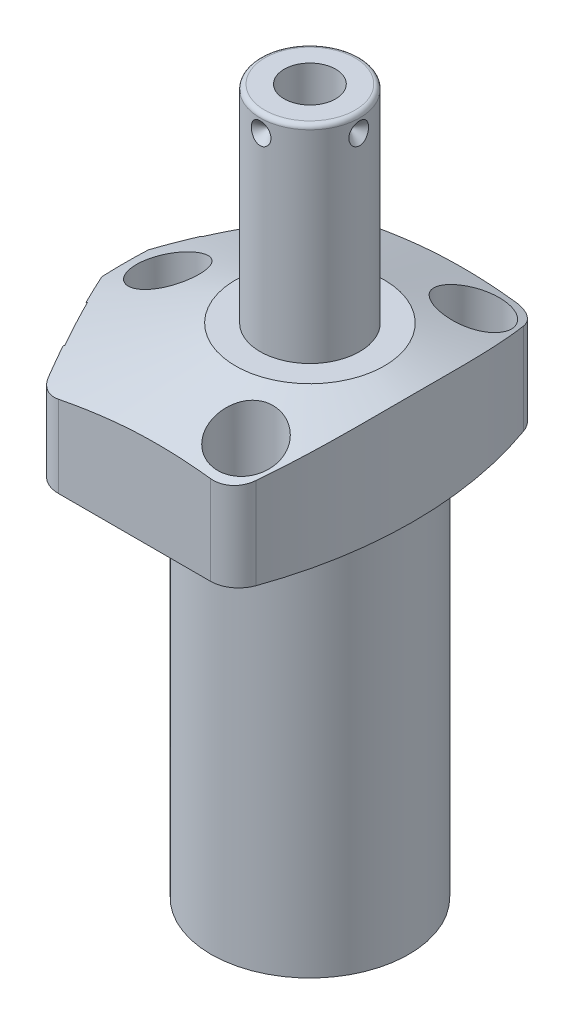
SolidWorks part; units mm, degrees
material "Alloy Steel"
ref_plane "Front Plane" through (0, 0, 0) normal (0, 0, 1) x (1, 0, 0)
ref_plane "Top Plane" through (0, 0, 0) normal (0, 1, 0) x (1, 0, 0)
ref_plane "Right Plane" through (0, 0, 0) normal (1, 0, 0) x (0, 0, -1)
ref_plane "Plane1" through (0, 0, 0) normal (0, 0, 1) x (0, -1, 0)
sketch "Sketch1" plane through (0, 0, 0) normal (0, 0, 1) x (0, -1, 0)
  line L0 (0, 44.45) -> (-26.9748, 44.45)
  line L1 (-26.9748, 44.45) -> (-26.9748, 0)
  line L2 (-26.9748, 0) -> (84.1502, 0)
  line L3 (84.1502, 0) -> (84.1502, 22.098)
  line L4 (84.1502, 22.098) -> (0, 22.098)
  line L5 (0, 22.098) -> (0, 44.45)
  line L6 (-32.531, 0) -> (89.7065, 0) construction
  dimension "D1" = 111.125
  dimension "D2" = 26.9748
  dimension "D3" = 88.9
  dimension "D4" = 44.196
revolve "Revolve1" add sketch "Sketch1" angle 360 about L6
ref_plane "Plane2" through (0, 0, 0) normal (0, -1, 0) x (0, 0, -1)
sketch "Sketch2" plane through (0, 0, 0) normal (0, -1, 0) x (0, 0, -1)
  line L0 (34.1122, -28.4984) -> (34.1122, 28.4984)
  line L2 (-34.1122, 28.4984) -> (-34.1122, -28.4984)
  line L3 (0, -32.1458) -> (0, 48.0974) construction
  arc A0 (34.1122, -28.4984) -> (34.1122, 28.4984) centre (0, 0) ccw
  circle A1 centre (0, 0) radius 44.45
  arc A2 (-34.1122, 28.4984) -> (-34.1122, -28.4984) centre (0, 0) ccw
  point P4 (0, 0)
  dimension "D1" = 68.2244
  dimension "D2" = 0
extrude "Cut-Extrude1" cut sketch "Sketch2" against normal up to next
ref_plane "Plane3" through (0, 0, 0) normal (0, -1, 0) x (-1, 0, 0)
sketch "Sketch3" plane through (0, 0, 0) normal (0, -1, 0) x (-1, 0, 0)
  line L0 (25.9049, 34.1122) -> (44.0427, 0)
  line L1 (44.0427, 0) -> (25.9049, -34.1122)
  line L2 (-39.4859, -20.995) -> (73.8214, 39.2515) construction
  line L3 (0, 0) -> (44.0427, 0) construction
  line L6 (-28.4984, -34.1122) -> (28.4984, -34.1122)
  line L7 (28.4984, 34.1122) -> (-28.4984, 34.1122)
  line L8 (25.9049, -34.1122) -> (28.4984, -34.1122)
  line L9 (28.4984, 34.1122) -> (25.9049, 34.1122)
  arc A2 (-28.4984, 34.1122) -> (-28.4984, -34.1122) centre (0, 0) ccw
  arc A3 (28.4984, -34.1122) -> (28.4984, 34.1122) centre (0, 0) ccw
  arc A5 (28.4984, -34.1122) -> (28.4984, 34.1122) centre (0, 0) ccw
  dimension "D1" = 28
  dimension "D2" = 38.8874
  dimension "D3" = 0
extrude "Cut-Extrude2" cut sketch "Sketch3" against normal up to next
ref_plane "Plane4" through (0, 0, 0) normal (0, -1, 0) x (-1, 0, 0)
sketch "S2D0002" plane through (0, 0, 0) normal (0, -1, 0) x (-1, 0, 0)
  line L0 (41.275, 85.425) -> (41.275, -85.425)
  arc A0 (41.275, 85.425) -> (41.275, -85.425) centre (65.8876, 0) ccw
  dimension "D3" = 88.9
  dimension "D1" = 65.8876
  dimension "D2" = 41.275
extrude "Cut-Extrude3" cut sketch "S2D0002" against normal blind 38.0873 flip side to cut
fillet "Fillet1" radius 6.35 2 edges at (16.2073, 13.4874, 34.1122) (16.2073, 13.4874, -34.1122)
fillet "Fillet2" radius 6.35 1 edges at (-25.9049, 13.4874, 34.1122)
fillet "Fillet3" radius 6.35 1 edges at (-25.9049, 13.4874, -34.1122)
ref_plane "Plane5" through (0, 0, 0) normal (0, 0, 1) x (1, 0, 0)
sketch "Sketch5" plane through (0, 0, 0) normal (0, 0, 1) x (1, 0, 0)
  line L0 (-16.637, 26.9748) -> (-47.625, 15.6961)
  line L1 (0, 7.6649) -> (0, 27.5963) construction
  line L3 (11.854, 26.9748) -> (-22.0895, 26.9748) construction
  line L4 (-16.637, 26.9748) -> (-47.625, 26.9748)
  line L5 (-47.625, 26.9748) -> (-47.625, 15.6961)
  dimension "D1" = 33.274
  dimension "D2" = 20
  dimension "D3" = 47.625
revolve "Cut-Revolve1" cut sketch "Sketch5" angle 360 about L1
ref_plane "Plane6" through (-34.1113, 10.287, -18.1373) normal (0, 1, 0) x (0.4695, 0, -0.8829)
sketch "Sketch6" plane through (-34.1113, 10.287, -18.1373) normal (0, 1, 0) x (0.4695, 0, -0.8829)
  line L0 (0, 0) -> (6.1849, 0)
  line L1 (6.1849, 0) -> (5.6423, -2.5527)
  line L2 (5.6423, -2.5527) -> (4.9784, -3.2166)
  line L3 (4.9784, -3.2166) -> (4.9784, -15.748)
  line L4 (4.9784, -15.748) -> (0, -15.748)
  line L5 (0, -15.748) -> (0, 0)
  line L6 (0, -16.5354) -> (0, 0.7874) construction
  dimension "D1" = 15.748
revolve "Cut-Revolve2" cut sketch "Sketch6" angle 360 about L6
ref_plane "Plane7" through (-34.1113, 10.287, 18.1373) normal (0, 1, 0) x (-0.4695, 0, -0.8829)
sketch "Sketch7" plane through (-34.1113, 10.287, 18.1373) normal (0, 1, 0) x (-0.4695, 0, -0.8829)
  line L0 (0, 0) -> (6.1849, 0)
  line L1 (6.1849, 0) -> (5.6423, -2.5527)
  line L2 (5.6423, -2.5527) -> (4.9784, -3.2166)
  line L3 (4.9784, -3.2166) -> (4.9784, -15.748)
  line L4 (4.9784, -15.748) -> (0, -15.748)
  line L5 (0, -15.748) -> (0, 0)
  line L6 (0, -16.5354) -> (0, 0.7874) construction
  dimension "D1" = 15.748
revolve "Cut-Revolve3" cut sketch "Sketch7" angle 360 about L6
ref_plane "Plane8" through (-13.4874, 2.667, -26.5938) normal (0, 0, 1) x (-1, 0, 0)
sketch "Sketch8" plane through (-13.4874, 2.667, -26.5938) normal (0, 0, 1) x (-1, 0, 0)
  line L0 (0, 0) -> (4.5466, 0)
  line L1 (4.5466, 0) -> (4.1066, -2.0701)
  line L2 (4.1066, -2.0701) -> (3.4544, -2.7223)
  line L3 (3.4544, -2.7223) -> (3.4544, -12.573)
  line L4 (3.4544, -12.573) -> (0, -12.573)
  line L5 (0, -12.573) -> (0, 0)
  line L6 (0, -13.2017) -> (0, 0.6287) construction
  dimension "D1" = 12.573
revolve "Cut-Revolve4" cut sketch "Sketch8" angle 360 about L6
ref_plane "Plane9" through (-13.4874, 2.667, 26.5938) normal (0, 0, 1) x (-1, 0, 0)
sketch "Sketch9" plane through (-13.4874, 2.667, 26.5938) normal (0, 0, 1) x (-1, 0, 0)
  line L0 (0, 0) -> (4.5466, 0)
  line L1 (4.5466, 0) -> (4.1066, -2.0701)
  line L2 (4.1066, -2.0701) -> (3.4544, -2.7223)
  line L3 (3.4544, -2.7223) -> (3.4544, -12.573)
  line L4 (3.4544, -12.573) -> (0, -12.573)
  line L5 (0, -12.573) -> (0, 0)
  line L6 (0, -13.2017) -> (0, 0.6287) construction
  dimension "D1" = 12.573
revolve "Cut-Revolve5" cut sketch "Sketch9" angle 360 about L6
sketch "Sketch17" plane through (-34.3355, 0, 18.2565) normal (-0.8829, 0, 0.4695) x (0.4695, 0, 0.8829)
  circle A0 centre (0, 10.287) radius 10.4775
  dimension "D1" = 20.955
extrude "Cut-Extrude4" cut sketch "Sketch17" against normal blind 0.254
sketch "Sketch18" plane through (0, 0, 0) normal (0, -1, 0) x (1, 0, 0)
  circle A0 centre (-13.4874, 26.5938) radius 5.5626
  dimension "D1" = 11.1252
extrude "Cut-Extrude5" cut sketch "Sketch18" against normal blind 2.667
mirror "Mirror1" about plane through (0, 0, 0) normal (0, 0, 1) of "Cut-Extrude5", "Cut-Extrude4"
ref_plane "Plane10" through (0, 0, 0) normal (1, 0, 0) x (0, 0, -1)
sketch "Sketch10" plane through (0, 0, 0) normal (1, 0, 0) x (0, 0, -1)
  line L0 (0, 26.9748) -> (-11.1125, 26.9748)
  line L1 (-11.1125, 26.9748) -> (-11.1125, 72.1868)
  line L2 (-10.0965, 73.2028) -> (0, 73.2028)
  line L3 (0, 73.2028) -> (0, 26.9748)
  line L4 (0, 14.3517) -> (0, 66.7398) construction
  line L5 (16.637, 26.9748) -> (-16.637, 26.9748) construction
  line L6 (-29.8978, 0) -> (29.8978, 0) construction
  arc A0 (-10.0965, 73.2028) -> (-11.1125, 72.1868) centre (-10.0965, 72.1868) ccw
  dimension "D2" = 1.016
  dimension "D1" = 73.2028
  dimension "D3" = 22.225
revolve "Revolve2" add sketch "Sketch10" angle 360 about L4
ref_plane "Plane11" through (5.7531, 64.8462, 0) normal (0, 0, 1) x (1, 0, 0)
sketch "S2D0001" plane through (5.7531, 64.8462, 0) normal (0, 0, 1) x (1, 0, 0)
  line L0 (0, 8.3566) -> (0, -8.6614)
  line L1 (0, -8.6614) -> (-5.7531, -12.1182)
  line L2 (0, 8.3566) -> (-5.7531, 8.3566)
  line L3 (-5.7531, 8.3566) -> (-5.7531, -12.1182)
  line L4 (-5.7531, -27.7363) -> (-5.7531, 1.0237) construction
  line L5 (4.3434, 8.3566) -> (-15.8496, 8.3566) construction
  dimension "D1" = 11.5062
  dimension "D2" = 17.018
  dimension "D3" = 59
revolve "Cut-Revolve6" cut sketch "S2D0001" angle 360 about L4
ref_plane "Plane13" through (-13.4874, 0, 26.5938) normal (1, 0, 0) x (0, 0, -1)
sketch "Sketch14" plane through (-13.4874, 0, 26.5938) normal (1, 0, 0) x (0, 0, -1)
  line L0 (5.461, 2.667) -> (5.461, 0.9398)
  line L1 (5.461, 0.9398) -> (5.3016, 0.9398)
  line L2 (2.667, 0.4318) -> (2.667, 0.127)
  line L3 (2.667, 0.127) -> (1.5875, 0.127)
  line L4 (1.5875, 0.127) -> (1.5875, 10.6172)
  line L5 (1.5875, 10.6172) -> (3.2512, 10.6172)
  line L6 (3.2512, 10.6172) -> (3.2512, 2.667)
  line L7 (3.2512, 2.667) -> (5.461, 2.667)
  line L8 (3.175, 0.9398) -> (3.8424, 0.9398)
  line L9 (0, -1.0109) -> (0, 11.1709) construction
  arc A0 (3.175, 0.9398) -> (2.667, 0.4318) centre (3.175, 0.4318) ccw
  arc A1 (3.8424, 0.9398) -> (5.3016, 0.9398) centre (4.572, 0.4318) ccw
  dimension "D1" = 2.54
  dimension "D2" = 7.9502
revolve "Revolve3" add sketch "Sketch14" angle 360 about L9
ref_plane "Plane14" through (-11.1125, 60.8838, 0) normal (0, 0, 1) x (0, 1, 0)
ref_plane "Plane15" through (0, 0, 0) normal (-0.7071, 0, 0.7071) x (0.7071, 0, 0.7071)
sketch "Sketch15" plane through (11.1125, 60.8838, 0) normal (0, 0, -1) x (0, 1, 0)
  line L0 (8.3566, 0) -> (10.7696, 0)
  line L1 (10.7696, 0) -> (8.3566, -2.413)
  line L2 (8.3566, 0) -> (8.3566, -2.413)
  line L3 (8.3566, -5.1094) -> (8.3566, 0.1207) construction
  line L4 (11.303, 0) -> (-33.909, 0) construction
  line L5 (12.319, -21.209) -> (12.319, -1.016) construction
  dimension "D1" = 3.9624
  dimension "D2" = 4.826
  dimension "D3" = 45
revolve "Cut-Revolve7" cut sketch "Sketch15" angle 360 about L3
hole_wizard "Hole1" positions "Sketch20" profile "Sketch19" legacy end condition up to next
sketch "Sketch20" plane through (0, 26.9748, 0) normal (0, 1, 0) x (-1, 0, 0)
  line L0 (0, 0) -> (47.6205, 0) construction
  line L1 (0, 0) -> (0, 38.9977) construction
  point P0 (-11.1252, -25.4)
  point P10 (31.75, 0)
  point P14 (-11.1252, 25.4)
  dimension "D1" = 11.1252
  dimension "D2" = 25.4
  dimension "D3" = 31.75
sketch "Sketch19" plane through (11.1252, 26.9748, -25.4) normal (1, 0, 0) x (0, 0, 1)
  line L0 (0, 0) -> (0, 26.9748)
  line L1 (0, 26.9748) -> (4.3688, 26.9748)
  line L2 (4.3688, 26.9748) -> (4.3688, 16.6624)
  line L3 (4.3688, 16.6624) -> (6.9977, 16.6624)
  line L4 (6.9977, 16.6624) -> (6.9977, 0)
  line L5 (6.9977, 0) -> (0, 0)
  line L6 (0, 110) -> (0, -10) construction
  dimension "Diameter" = 8.7376
  dimension "Depth" = 26.9748
  dimension "C-Bore Diameter" = 13.9954
  dimension "C-Bore Depth" = 16.6624
mirror "Mirror2" about plane through (0, 0, 0) normal (0, 0, 1) of "Revolve3"
pattern_circular "CirPattern1" count 4 over 360 about axis through (0, 14.3517, 0) along (0, -1, 0) of "Cut-Revolve7"
